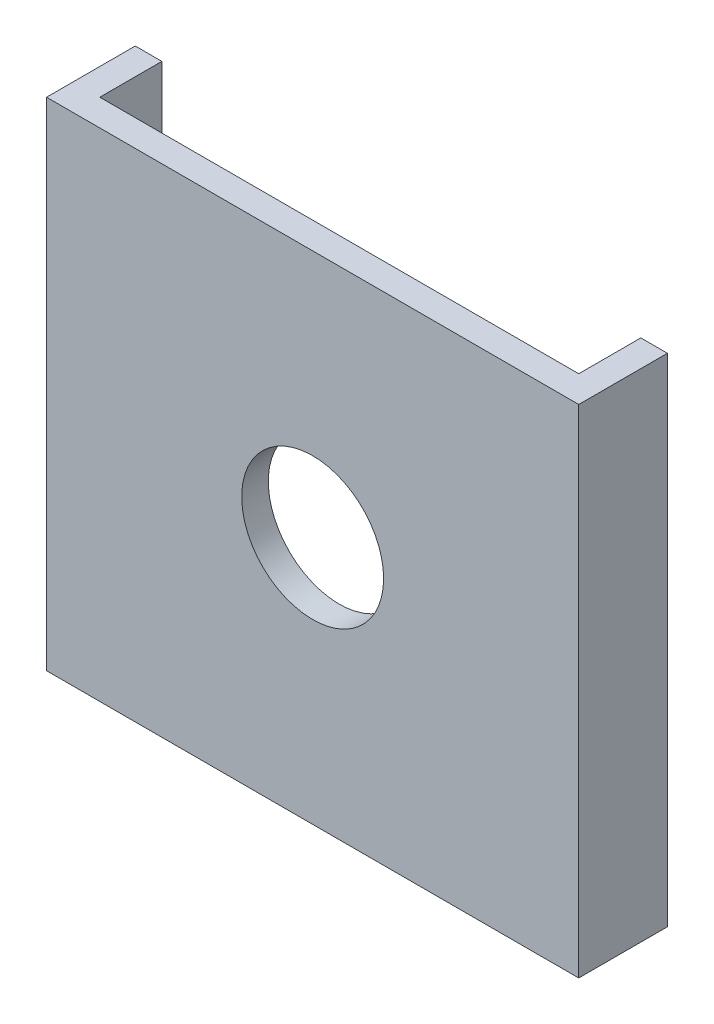
SolidWorks part; units mm, degrees
ref_plane "前视基准面" through (0, 0, 0) normal (0, 0, 1) x (1, 0, 0)
ref_plane "上视基准面" through (0, 0, 0) normal (0, 1, 0) x (1, 0, 0)
ref_plane "右视基准面" through (0, 0, 0) normal (1, 0, 0) x (0, 0, -1)
sketch "草图1" plane through (0, 0, 0) normal (0, 1, 0) x (1, 0, 0)
  line L0 (-15, 0) -> (15, 0)
  line L1 (15, 0) -> (15, 5)
  line L2 (13.5, 5) -> (15, 5)
  line L4 (13.5, 5) -> (13.5, 1.5)
  line L5 (13.5, 1.5) -> (-13.5, 1.5)
  line L6 (-13.5, 1.5) -> (-13.5, 5)
  line L7 (-13.5, 5) -> (-15, 5)
  line L8 (-15, 5) -> (-15, 0)
  dimension "D1" = 30
  dimension "D2" = 15
  dimension "D3" = 1.5
  dimension "D4" = 1.5
  dimension "D5" = 1.5
  dimension "D6" = 5
  dimension "D7" = 5
extrude "凸台-拉伸1" add sketch "草图1" along normal blind 28
sketch "草图2" plane through (-15, 0, 0) normal (-1, 0, 0) x (0, 0, 1)
  line L0 (-5, 28) -> (-5, 0) construction
  line L2 (-8, 19) -> (-5, 19)
  line L3 (-5, 19) -> (-5, 9)
  line L4 (-5, 9) -> (-8, 9)
  arc A0 (-8, 19) -> (-8, 9) centre (-8, 14) ccw
  dimension "D1" = 10
  dimension "D2" = 14
  dimension "D3" = 3
extrude "凸台-拉伸2" add sketch "草图2" against normal blind 1.5 separate body
sketch "草图3" plane through (-13.5, 0, 0) normal (1, 0, 0) x (0, 0, -1)
  circle A0 centre (8, 14) radius 1.55
extrude "切除-拉伸1" cut sketch "草图3" against normal blind 1.5
sketch "草图4" plane through (0, 0, 0) normal (0, 0, 1) x (1, 0, 0)
  line L0 (-15, 28) -> (15, 28) construction
  line L1 (15, 28) -> (15, 0) construction
  circle A0 centre (0, 14) radius 4
  dimension "D1" = 8
  dimension "D2" = 14
  dimension "D3" = 15
extrude "切除-拉伸2" cut sketch "草图4" against normal blind 1.5
